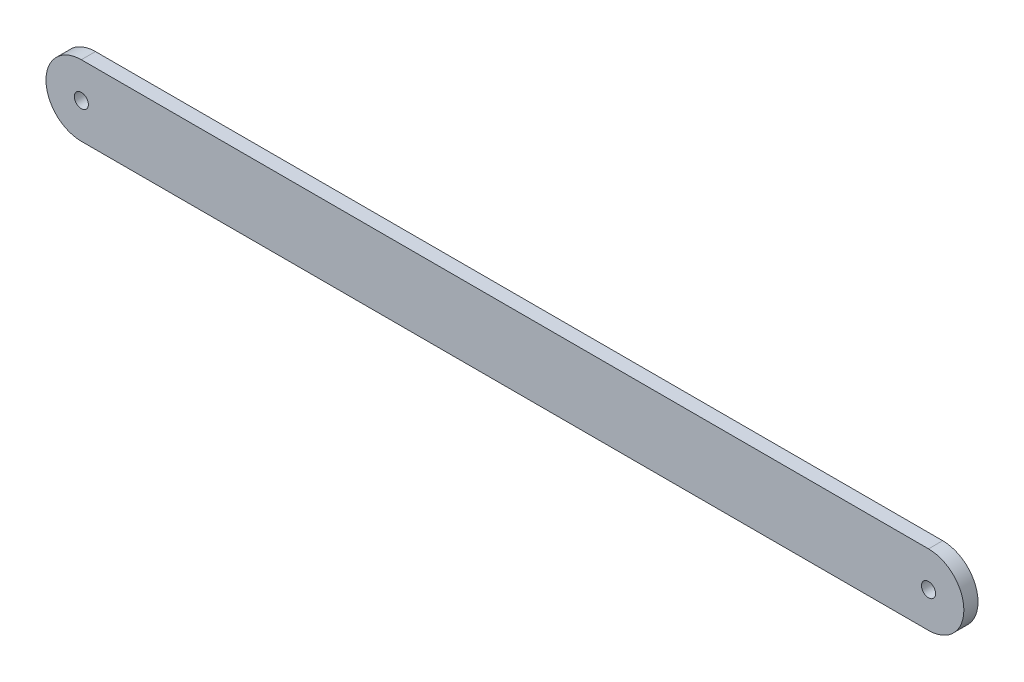
SolidWorks part; units mm, degrees
ref_plane "前视基准面" through (0, 0, 0) normal (0, 0, 1) x (1, 0, 0)
ref_plane "上视基准面" through (0, 0, 0) normal (0, 1, 0) x (1, 0, 0)
ref_plane "右视基准面" through (0, 0, 0) normal (1, 0, 0) x (0, 0, -1)
sketch "草图1" plane through (0, 0, 0) normal (0, 0, 1) x (1, 0, 0)
  line L1 (119.76, -10) -> (-120, -10)
  line L3 (119.76, 10) -> (-120, 10)
  arc A0 (-120, 10) -> (-120, -10) centre (-120, 0) ccw
  arc A1 (119.76, -10) -> (119.76, 10) centre (119.76, 0) ccw
  circle A2 centre (-120, 0) radius 2
  circle A3 centre (119.76, 0) radius 2
  point P0 (0, 0)
  dimension "D3" = 4
  dimension "D4" = 4
  dimension "D5" = 10
  dimension "D1" = 20
  dimension "D2" = 239.76
extrude "凸台-拉伸1" add sketch "草图1" along normal blind 4
